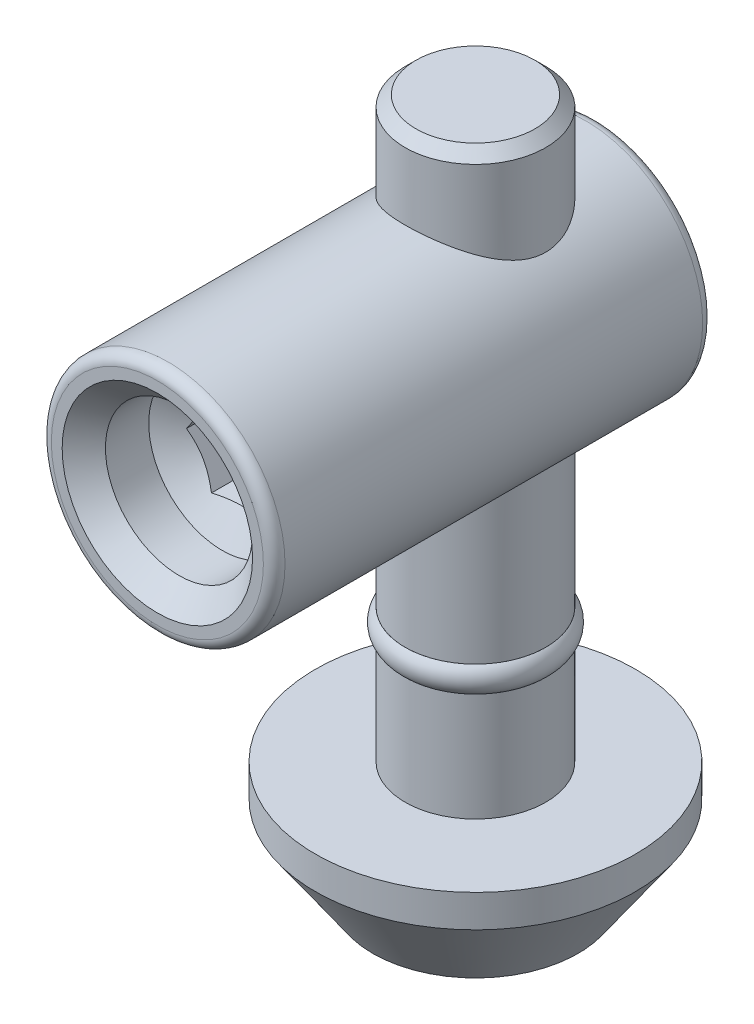
SolidWorks part; units mm, degrees
ref_plane "Спереди" through (0, 0, 0) normal (0, 0, 1) x (1, 0, 0)
ref_plane "Сверху" through (0, 0, 0) normal (0, 1, 0) x (1, 0, 0)
ref_plane "Справа" through (0, 0, 0) normal (1, 0, 0) x (0, 0, -1)
sketch "Эскиз3" plane through (0, 0, 0) normal (0, 0, 1) x (1, 0, 0)
  line L0 (0, 0) -> (-3.25, 0)
  line L1 (-3.25, 0) -> (-3.25, -20.5)
  line L2 (-3.25, -20.5) -> (-2.75, -20.5)
  line L3 (-2.75, -20.5) -> (-2.75, -21.7)
  line L4 (-2.75, -21.7) -> (-3.25, -21.7)
  line L5 (-3.25, -21.7) -> (-3.25, -26.7)
  line L7 (0, -32) -> (0, 0)
  line L8 (0, 0) -> (0, 5.384) construction
  line L9 (-3.25, -26.7) -> (-7.4, -26.7)
  line L10 (-7.4, -26.7) -> (-7.4, -28.2)
  line L11 (-7.4, -28.2) -> (-4.75, -32)
  line L12 (-4.75, -32) -> (0, -32)
  dimension "D1" = 6.5
  dimension "D2" = 1.2
  dimension "D3" = 32
  dimension "D4" = 0.5
  dimension "D5" = 5
  dimension "D6" = 5.3
  dimension "D7" = 1.5
  dimension "D8" = 1.5
  dimension "D9" = 14.8
revolve "Повернуть1" add sketch "Эскиз3" angle 360 about L8
chamfer "Фаска1" distance 0.5 angle 45 1 edges at (0, 0, -3.25)
sketch "Эскиз12" plane through (0, 0, 0) normal (0, 0, 1) x (1, 0, 0)
  line L0 (2.75, 0) -> (-2.75, 0) construction
  circle A0 centre (0, -9) radius 5.4
  dimension "D1" = 10.8
  dimension "D2" = 9
extrude "Бобышка-Вытянуть2" add sketch "Эскиз12" along normal blind 14.7 and the other way blind 5.6
hole_wizard "Отверстие обработанное метчиком M81" positions "Эскиз13" profile "Эскиз14" tap size "M8" standard "ISO"
sketch "Эскиз13" plane through (0, 0, 14.7) normal (0, 0, 1) x (1, 0, 0)
  point P0 (0, -9)
cosmetic thread "Отверстие резьбы1" parameters "D1"=3, "D2"=8
sketch "Эскиз14" plane through (0, -9, 14.7) normal (1, 0, 0) x (0, -1, 0)
  line L0 (0, 0) -> (0, 5.0429)
  line L1 (0, 5.0429) -> (3.4, 3)
  line L2 (3.4, 3) -> (3.4, 1)
  line L3 (3.4, 1) -> (4.4, 0)
  line L5 (4.4, 0) -> (0, 0)
  line L6 (-3.4, 1) -> (-4.4, 0) construction
  line L10 (0, 5.0429) -> (-3.4, 3) construction
  line L11 (0, -6.35) -> (0, 107.95) construction
  dimension "Диаметр сверла" = 6.8
  dimension "Глубина сверла" = 3
  dimension "Диаметр передней зенковки" = 8.8
  dimension "Угол передней зенковки" = 90
  dimension "Угол заточки сверла" = 118
fillet "Скругление1" radius 0.5 2 edges at (5.4, -9, -5.6) (5.4, -9, 14.7)
sketch "Эскиз15" plane through (0, 0, 14.7) normal (0, 0, 1) x (1, 0, 0)
  line L1 (2.3094, -9) -> (1.1547, -7)
  line L2 (1.1547, -7) -> (-1.1547, -7)
  line L3 (-1.1547, -7) -> (-2.3094, -9)
  line L4 (-2.3094, -9) -> (-1.1547, -11)
  line L5 (-1.1547, -11) -> (1.1547, -11)
  line L6 (1.1547, -11) -> (2.3094, -9)
  circle A0 centre (0, -9) radius 2 construction
  dimension "D1" = 4
extrude "Вырез-Вытянуть2" cut sketch "Эскиз15" against normal blind 6
sketch "Эскиз16" plane through (0, 0, 0) normal (0, 0, 1) x (1, 0, 0)
  line L0 (-2.75, -20.5) -> (-3.25, -20.5)
  line L1 (-2.75, -20.5) -> (-2.75, -21.7) construction
  line L2 (-3.25, -21.7) -> (-2.75, -21.7)
  line L3 (-2.75, -21.7) -> (-2.75, -20.5)
  line L4 (-2.75, -20.5) -> (2.75, -20.5) construction
  line L7 (-3.25, -13.3125) -> (-3.25, -20.5) construction
  line L8 (3.25, -21.7) -> (-3.25, -21.7) construction
  line L9 (0, -20.5) -> (0, -21.7) construction
  arc A0 (-3.25, -20.5) -> (-3.25, -21.7) centre (-2.75, -21.1) ccw
  point P15 (-2.75, -21.1)
revolve "Повернуть2" add sketch "Эскиз16" angle 360 about L9
